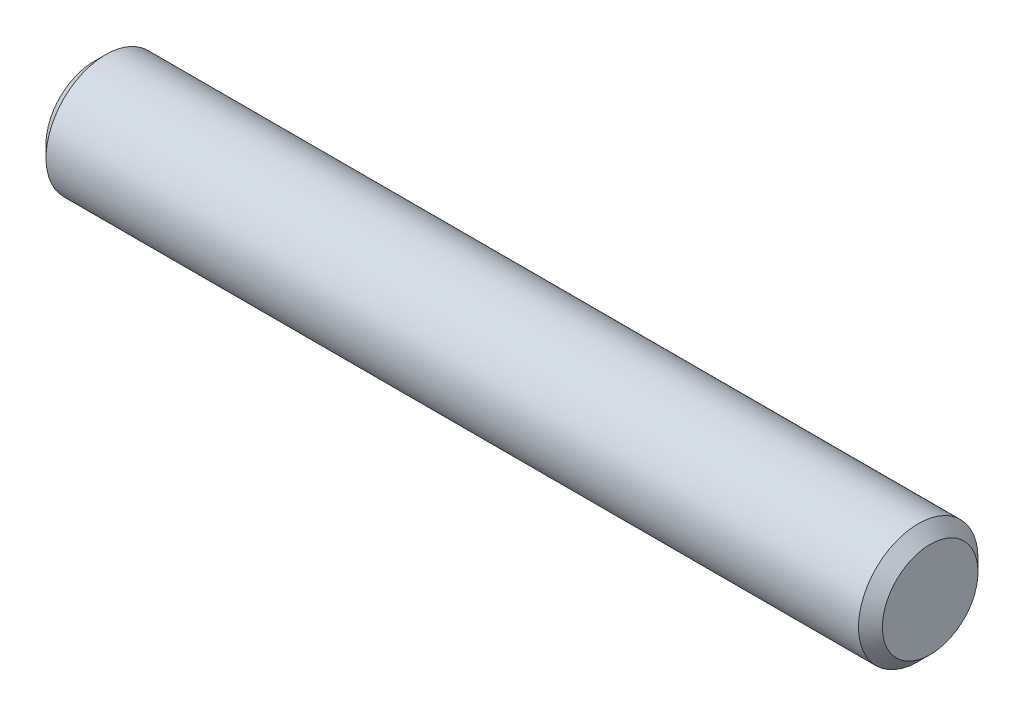
SolidWorks part; units mm, degrees
material "AISI 1020 Steel, Cold Rolled"
ref_plane "Front Plane" through (0, 0, 0) normal (0, 0, 1) x (1, 0, 0)
ref_plane "Top Plane" through (0, 0, 0) normal (0, 1, 0) x (1, 0, 0)
ref_plane "Right Plane" through (0, 0, 0) normal (1, 0, 0) x (0, 0, -1)
sketch "Sketch1" plane through (0, 0, 0) normal (0, 0, 1) x (1, 0, 0)
  line L0 (-22.225, 2.54) -> (-22.225, 0)
  line L1 (-22.225, 0) -> (22.225, 0)
  line L2 (22.225, 0) -> (22.225, 2.54)
  line L3 (22.225, 2.54) -> (21.59, 3.175)
  line L4 (21.59, 3.175) -> (-21.59, 3.175)
  line L5 (-21.59, 3.175) -> (-22.225, 2.54)
  line L6 (-22.225, 0) -> (22.225, 0) construction
  dimension "D1" = 3.175
  dimension "D2" = 44.45
  dimension "D3" = 45
  dimension "D4" = 0.635
  dimension "D5" = 45
revolve "Revolve1" add sketch "Sketch1" angle 360 about L6
